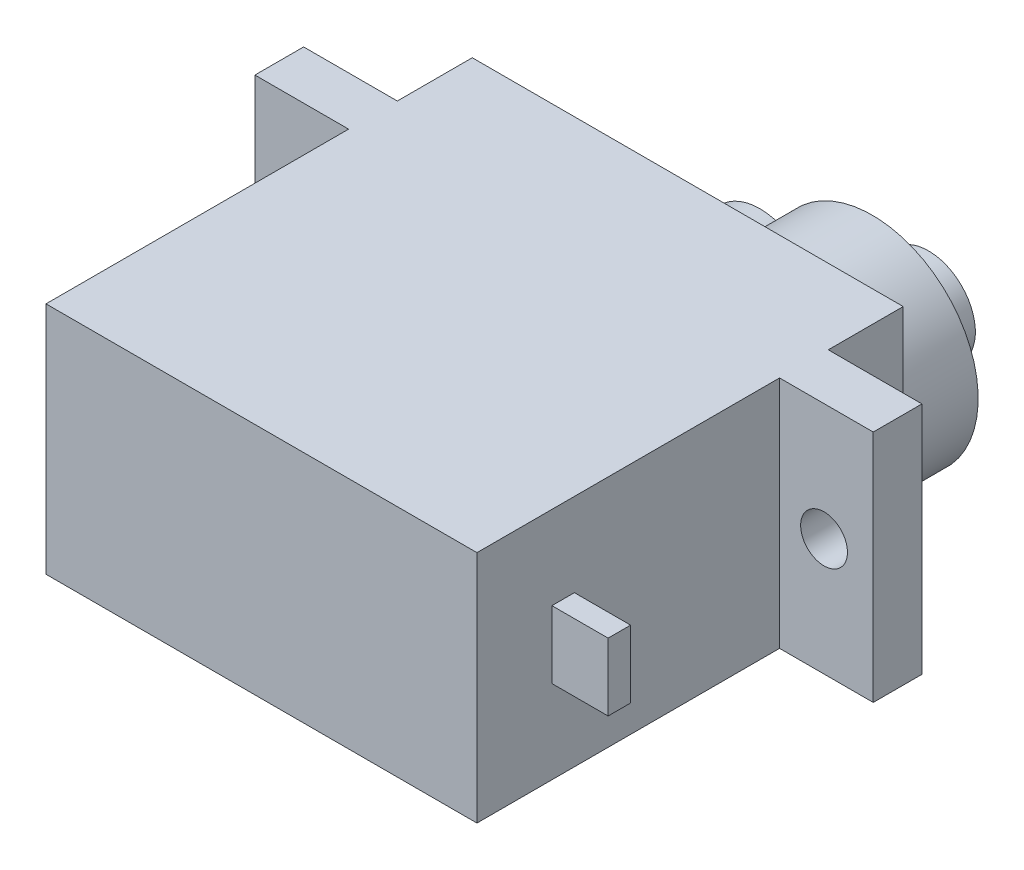
SolidWorks part; units mm, degrees
ref_plane "Спереди" through (0, 0, 0) normal (0, 0, 1) x (1, 0, 0)
ref_plane "Сверху" through (0, 0, 0) normal (0, 1, 0) x (1, 0, 0)
ref_plane "Справа" through (0, 0, 0) normal (1, 0, 0) x (0, 0, -1)
sketch "Эскиз1" plane through (0, 0, 0) normal (0, 1, 0) x (1, 0, 0)
  line L0 (0, 16.15) -> (-5, 16.15)
  line L1 (0, 0) -> (23, 0)
  line L2 (0, 0) -> (0, 22.75)
  line L3 (0, 22.75) -> (23, 22.75)
  line L4 (23, 0) -> (23, 22.75)
  line L5 (-5, 16.15) -> (-5, 18.75)
  line L6 (-5, 18.75) -> (0, 18.75)
  line L7 (23, 16.15) -> (28, 16.15)
  line L8 (28, 16.15) -> (28, 18.75)
  line L9 (28, 18.75) -> (23, 18.75)
  dimension "D1" = 23
  dimension "D2" = 22.75
  dimension "D3" = 2.6
  dimension "D5" = 5
  dimension "D6" = 5
  dimension "D7" = 4
extrude "Бобышка-Вытянуть1" add sketch "Эскиз1" along normal blind 12.5 contours L6 L5 L0 L2 | L1 L4 L3 L2 | L8 L9 L4 L7
sketch "Эскиз2" plane through (0, 0, -22.75) normal (0, 0, -1) x (-1, 0, 0)
  line L0 (0, 0) -> (-23, 0) construction
  line L1 (-23, 12.5) -> (-23, 0) construction
  circle A0 centre (-17.35, 6.25) radius 5.65
  dimension "D2" = 6.25
  dimension "D3" = 5.65
extrude "Бобышка-Вытянуть2" add sketch "Эскиз2" along normal blind 4
sketch "Эскиз3" plane through (0, 0, -26.75) normal (0, 0, -1) x (-1, 0, 0)
  circle A0 centre (-17.35, 6.25) radius 2.5
  circle A1 centre (-17.35, 6.25) radius 5.65 construction
  dimension "D1" = 5
  dimension "D2" = 0
  dimension "D3" = 0
extrude "Бобышка-Вытянуть3" add sketch "Эскиз3" along normal blind 3
sketch "Эскиз4" plane through (0, 0, -29.75) normal (0, 0, -1) x (-1, 0, 0)
  circle A0 centre (-17.35, 6.25) radius 0.9
  dimension "D1" = 1.8
extrude "Вырез-Вытянуть1" cut sketch "Эскиз4" against normal blind 6.5
sketch "Эскиз5" plane through (0, 0, -22.75) normal (0, 0, -1) x (-1, 0, 0)
  line L1 (0, 12.5) -> (-23, 12.5) construction
  circle A0 centre (-11.35, 6.25) radius 2.95
  circle A1 centre (-17.35, 6.25) radius 5.65 construction
  dimension "D1" = 5.9
  dimension "D2" = 6
  dimension "D3" = 6.25
extrude "Бобышка-Вытянуть4" add sketch "Эскиз5" along normal blind 4
sketch "Эскиз6" plane through (0, 0, -18.75) normal (0, 0, -1) x (-1, 0, 0)
  line L0 (5, 12.5) -> (0, 12.5) construction
  line L3 (-28, 0) -> (-23, 0) construction
  line L4 (2.375, 6.25) -> (5, 6.25) construction
  line L7 (-28, 6.25) -> (-25.375, 6.25) construction
  line L8 (5, 12.5) -> (5, 0) construction
  line L10 (-28, 12.5) -> (-28, 0) construction
  circle A0 centre (2.375, 6.25) radius 1.25
  circle A1 centre (-25.375, 6.25) radius 1.25
  dimension "D1" = 2.5
  dimension "D4" = 2.5
  dimension "D2" = 6.25
  dimension "D3" = 27.75
  dimension "D6" = 6.25
extrude "Вырез-Вытянуть2" cut sketch "Эскиз6" against normal up to next
sketch "Эскиз7" plane through (23, 0, 0) normal (1, 0, 0) x (0, 0, -1)
  line L0 (0, 12.5) -> (16.15, 12.5) construction
  line L1 (4, 8.05) -> (5.2, 8.05)
  line L2 (4, 8.05) -> (4, 4.45)
  line L3 (4, 4.45) -> (5.2, 4.45)
  line L4 (5.2, 8.05) -> (5.2, 4.45)
  line L15 (0, 12.5) -> (0, 0) construction
  dimension "D1" = 3.6
  dimension "D2" = 1.2
  dimension "D3" = 4.45
  dimension "D4" = 4
extrude "Бобышка-Вытянуть5" add sketch "Эскиз7" along normal blind 3
